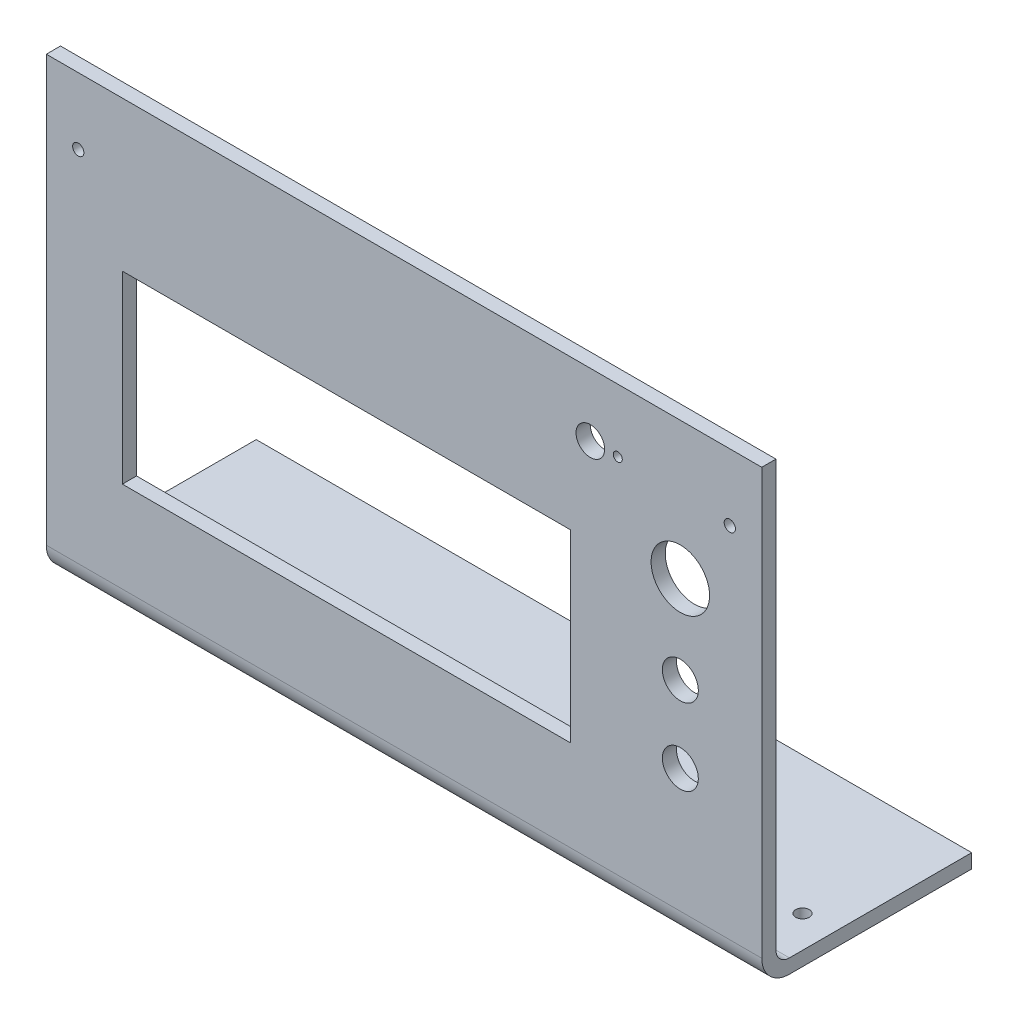
SolidWorks part; units mm, degrees
material "Acrylic (Medium-high impact)"
ref_plane "Front Plane" through (0, 0, 0) normal (0, 0, 1) x (1, 0, 0)
ref_plane "Top Plane" through (0, 0, 0) normal (0, 1, 0) x (1, 0, 0)
ref_plane "Right Plane" through (0, 0, 0) normal (1, 0, 0) x (0, 0, -1)
sketch "Sketch22" plane through (0, 0, 0) normal (0, 0, 1) x (1, 0, 0)
  line L2 (10.6, -42.5) -> (-134.4, -42.5) construction
  line L3 (10.6, -42.5) -> (10.6, 7.5) construction
  line L4 (10.6, 7.5) -> (-134.4, 7.5) construction
  line L5 (-134.4, -42.5) -> (-134.4, 7.5) construction
  line L6 (10.6, -42.5) -> (-134.4, 7.5) construction
  line L7 (10.6, 7.5) -> (-134.4, -42.5) construction
  line L8 (-140.9, 30.5) -> (18.1, 30.5)
  line L9 (-124, -2.8) -> (-24.4, -2.8)
  line L10 (-124, -2.8) -> (-124, -43.8)
  line L11 (-124, -43.8) -> (-24.4, -43.8)
  line L12 (-24.4, -2.8) -> (-24.4, -43.8)
  line L13 (-124, -2.8) -> (-24.4, -43.8) construction
  line L14 (-124, -43.8) -> (-24.4, -2.8) construction
  line L15 (-24.4, -48.8) -> (-124, -48.8) construction
  line L16 (-24.4, -48.8) -> (-24.4, 12.2) construction
  line L17 (-24.4, 12.2) -> (-124, 12.2) construction
  line L18 (-124, -48.8) -> (-124, 12.2) construction
  line L19 (-24.4, -48.8) -> (-124, 12.2) construction
  line L20 (-24.4, 12.2) -> (-124, -48.8) construction
  line L21 (-140.9, 30.5) -> (-140.9, -59.5)
  line L22 (-140.9, -59.5) -> (18.1, -59.5)
  line L23 (18.1, 30.5) -> (18.1, -59.5)
  circle A0 centre (-134.4, 7.5) radius 1.375 construction
  circle A1 centre (-134.4, -42.5) radius 1.375 construction
  circle A2 centre (10.6, -42.5) radius 1.375 construction
  circle A3 centre (10.6, 7.5) radius 1.375 construction
  circle A4 centre (0, -19.5) radius 4
  circle A5 centre (0, -36.5) radius 4
  circle A6 centre (0, 0) radius 6.5
  point P0 (-61.9, -17.5)
  point P12 (-74.2, -18.3)
  point P13 (-74.2, -23.3)
  dimension "D1" = 2.75
  dimension "D9" = 8
  dimension "D14" = 13
  dimension "D2" = 145
  dimension "D3" = 50
  dimension "D4" = 16.9
  dimension "D5" = 41
  dimension "D6" = 99.6
  dimension "D7" = 10.4
  dimension "D8" = 10.3
  dimension "D10" = 10.6
  dimension "D11" = 27
  dimension "D12" = 17
  dimension "D13" = 19.5
  dimension "D15" = 159
  dimension "D16" = 10
  dimension "D17" = 33.3
  dimension "D18" = 90
extrude "Boss-Extrude1" add sketch "Sketch22" along normal blind 3.15
sketch "Sketch23" plane through (-140.9, 0, 0) normal (-1, 0, 0) x (0, 0, 1)
  line L0 (0, -59.5) -> (3.15, -59.5)
  line L1 (3.15, -59.5) -> (3.15, -64)
  line L2 (-3, -70.15) -> (-43.5, -70.15)
  line L3 (-43.5, -70.15) -> (-43.5, -67)
  line L4 (0, -59.5) -> (0, -64)
  line L5 (-43.5, -67) -> (-3, -67)
  line L6 (0, 30.5) -> (0, -59.5) construction
  line L7 (3.15, 30.5) -> (0, 30.5) construction
  arc A0 (3.15, -64) -> (-3, -70.15) centre (-3, -64) cw
  arc A1 (-3, -67) -> (0, -64) centre (-3, -64) ccw
  dimension "D1" = 3
  dimension "D2" = 90
  dimension "D3" = 97.5
  dimension "D4" = 43.5
extrude "Boss-Extrude2" add sketch "Sketch23" against normal up to surface (159 mm away) up to face at (18.1, -14.5, 1.575)
sketch "Sketch25" plane through (0, 0, 3.15) normal (0, 0, 1) x (1, 0, 0)
  line L0 (18.1, 30.5) -> (-140.9, 30.5) construction
  line L2 (-61.4, 30.5) -> (-61.4, -28.7414) construction
  circle A0 centre (-133.8, 15.7) radius 1.25
  circle A1 centre (11, 15.7) radius 1.25
  point P4 (-61.4, 30.5)
  dimension "D1" = 14.8
  dimension "D2" = 72.4
  dimension "D3" = 2.5
extrude "Cut-Extrude1" cut sketch "Sketch25" against normal through all
sketch "Sketch26" plane through (0, -70.15, 0) normal (0, -1, 0) x (1, 0, 0)
  line L0 (18.1, 3.15) -> (-140.9, 3.15) construction
  line L1 (18.1, -43.5) -> (-140.9, -43.5) construction
  line L3 (18.1, 3.15) -> (-140.9, 3.15) construction
  line L4 (-61.4, -43.5) -> (-61.4, 14.0341) construction
  circle A0 centre (-133.8, -13) radius 1.5
  circle A1 centre (11, -13) radius 1.5
  point P6 (-61.4, 3.15)
  dimension "D1" = 3
  dimension "D2" = 16.15
  dimension "D3" = 72.4
extrude "Cut-Extrude2" cut sketch "Sketch26" against normal through all
sketch "Sketch27" plane through (-140.9, 0, 0) normal (-1, 0, 0) x (0, 0, 1)
  line L0 (0, 30.5) -> (0, -64) construction
  line L1 (-3, -67) -> (-43.5, -67) construction
  line L2 (0, 30.5) -> (0, -64)
  line L3 (-3, -67) -> (-43.5, -67)
  line L4 (1.6, 30.5) -> (1.6, -64)
  line L5 (-3, -68.6) -> (-43.5, -68.6)
  arc A0 (-3, -67) -> (0, -64) centre (-3, -64) ccw construction
  arc A1 (-3, -67) -> (0, -64) centre (-3, -64) ccw
  arc A2 (-3, -68.6) -> (1.6, -64) centre (-3, -64) ccw
  dimension "D1" = 1.6
sketch "Sketch28" plane through (0, 0, 3.15) normal (0, 0, 1) x (1, 0, 0)
  circle A0 centre (-20, 16.5) radius 3.175
  circle A1 centre (0, 0) radius 6.5 construction
  circle A2 centre (-13.9, 16.5) radius 1
  dimension "D1" = 6.35
  dimension "D3" = 16.5
  dimension "D4" = 6.1
  dimension "D5" = 2
  dimension "D2" = 20
extrude "Cut-Extrude3" cut sketch "Sketch28" against normal through all
